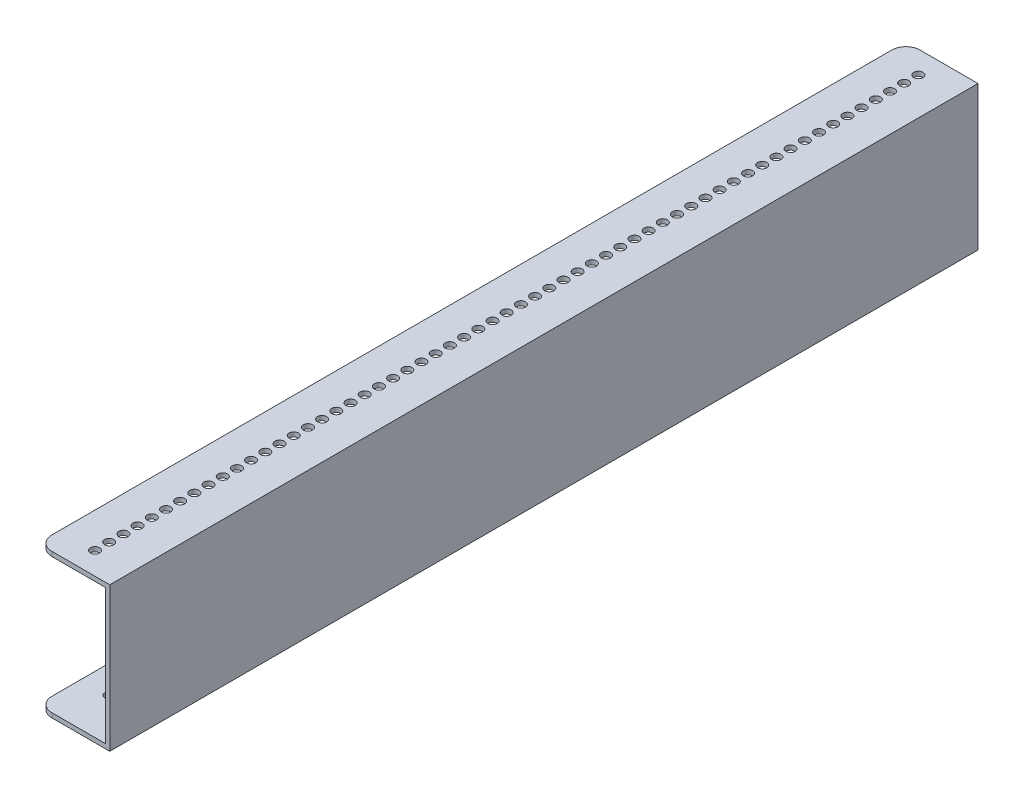
SolidWorks part; units mm, degrees
material "6061-T6 (SS)"
ref_plane "Front Plane" through (0, 0, 0) normal (0, 0, 1) x (1, 0, 0)
ref_plane "Top Plane" through (0, 0, 0) normal (0, 1, 0) x (1, 0, 0)
ref_plane "Right Plane" through (0, 0, 0) normal (1, 0, 0) x (0, 0, -1)
sketch "Sketch2" plane through (0, 0, 0) normal (0, 0, 1) x (1, 0, 0)
  line L0 (-304.8, 12.7) -> (-304.8, 15.875)
  line L1 (-304.8, 12.7) -> (-254, 12.7)
  line L3 (-254, 12.7) -> (-254, 114.3)
  line L4 (-254, 114.3) -> (-304.8, 114.3)
  line L5 (-304.8, 114.3) -> (-304.8, 111.125)
  line L6 (-304.8, 111.125) -> (-257.175, 111.125)
  line L7 (-257.175, 111.125) -> (-257.175, 15.875)
  line L8 (-257.175, 15.875) -> (-304.8, 15.875)
  dimension "D1" = 3.175
  dimension "D2" = 12.7
  dimension "D3" = 254
  dimension "D4" = 101.6
  dimension "D5" = 3.175
  dimension "D6" = 3.175
  dimension "D7" = 50.8
extrude " Alum C chnl LONGBoss-Extrude2" add sketch "Sketch2" along normal blind 305.8 and the other way blind 305.8 separate body
fillet "Fillet1" radius 10 4 edges at (-304.8, 112.7125, -305.8) (-304.8, 112.7125, 305.8) (-304.8, 14.2875, -305.8) (-304.8, 14.2875, 305.8)
sketch "Sketch7" plane through (0, 114.3, 0) normal (0, 1, 0) x (1, 0, 0)
  line L0 (-280.2, 282.3762) -> (-280.2, -282.3762) construction
  line L1 (-280.2, 0) -> (0, 0) construction
  line L2 (0, 0) -> (0, 304.8) construction
  line L3 (-254, 305.8) -> (-254, -305.8) construction
  line L4 (0, 0) -> (284.8, 0) construction
  circle A0 centre (-280.2, 0) radius 3.25
  dimension "D1" = 6.5
  dimension "D2" = 26.2
extrude "Cut-Extrude4" cut sketch "Sketch7" against normal blind 20
pattern_linear "LPattern2" count 30 spacing 10 along (0, 0, -1) of "Cut-Extrude4"
pattern_linear "LPattern1" count 30 spacing 10 along (0, 0, 1) of "Cut-Extrude4"
sketch "Sketch10" plane through (0, 15.875, 0) normal (0, 1, 0) x (1, 0, 0)
  line L0 (-285, -275) -> (-285, 0) construction
  line L1 (-285, 0) -> (-285, 275) construction
  line L2 (0, 0) -> (-281.75, 0) construction
  circle A0 centre (-285, 275) radius 3.25
  circle A1 centre (-285, 0) radius 3.25
  circle A2 centre (-285, -275) radius 3.25
  dimension "D1" = 6.5
  dimension "D2" = 275
  dimension "D3" = 285
extrude "Cut-Extrude8" cut sketch "Sketch10" against normal blind 3.175
sketch "Sketch11" plane through (0, 114.3, 0) normal (0, 1, 0) x (1, 0, 0)
  line L0 (-254, 305.8) -> (-254, -305.8) construction
  line L2 (-254, 0) -> (-304.8, 0) construction
  line L3 (-304.8, 295.8) -> (-304.8, -295.8) construction
  circle A0 centre (-265.6, -295.8) radius 2.75
  circle A1 centre (-265.6, 295.8) radius 2.75
  circle A2 centre (-294.8, 295.8) radius 2.75
  circle A3 centre (-280.2, 290) radius 3.25 construction
  circle A4 centre (-280.2, -290) radius 3.25 construction
  circle A5 centre (-280.2, 290) radius 3.25
  circle A6 centre (-280.2, -290) radius 3.25
  circle A7 centre (-294.8, -295.8) radius 2.75
  arc A10 (-294.8, 305.8) -> (-304.8, 295.8) centre (-294.8, 295.8) ccw construction
  arc A11 (-304.8, -295.8) -> (-294.8, -305.8) centre (-294.8, -295.8) ccw construction
  circle A12 centre (-265.6, 0) radius 2.75
  circle A13 centre (-294.8, 0) radius 2.75
  point P18 (-294.8, 0)
  point P19 (-265.6, 0)
  point P20 (-265.6, 0)
  dimension "D1" = 5.5
  dimension "D2" = 14.6
